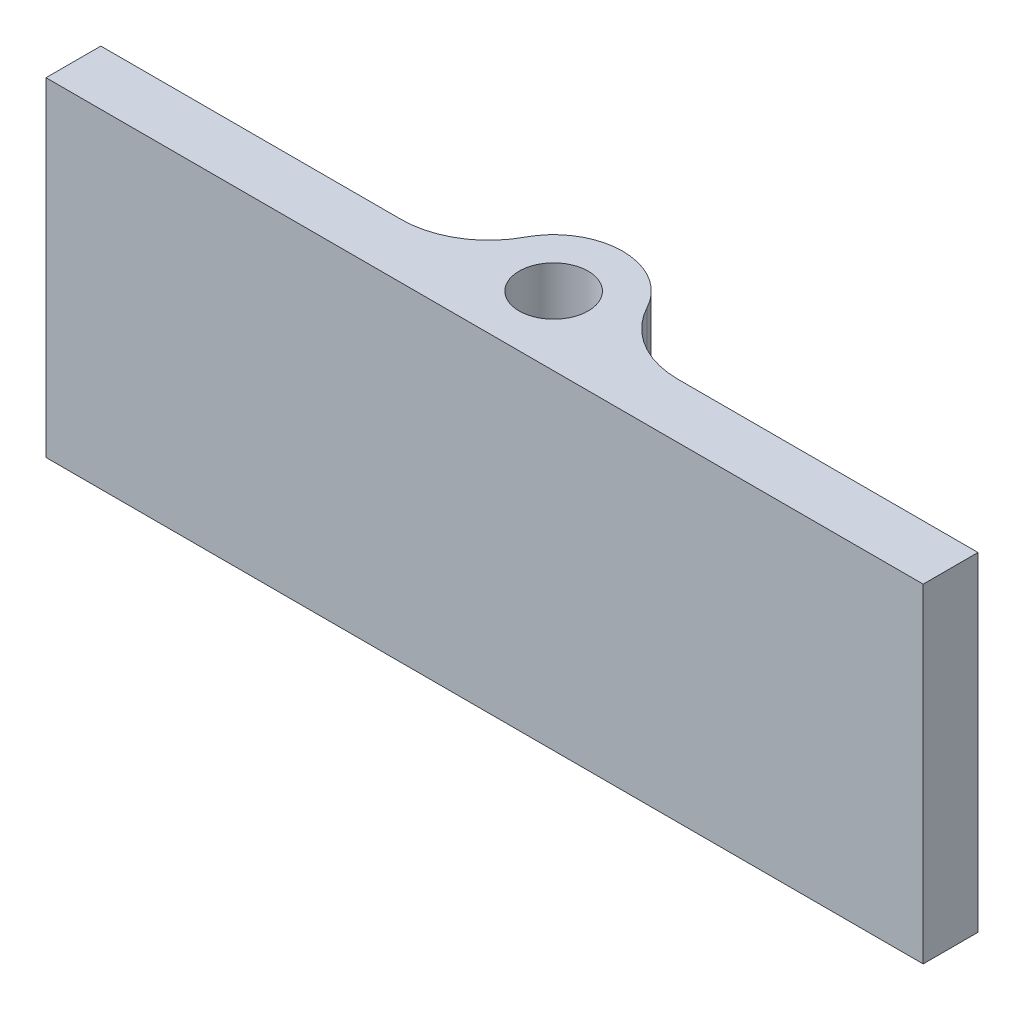
SolidWorks part; units mm, degrees
material "LWPLA"
ref_plane "Front Plane" through (0, 0, 0) normal (0, 0, 1) x (1, 0, 0)
ref_plane "Top Plane" through (0, 0, 0) normal (0, 1, 0) x (1, 0, 0)
ref_plane "Right Plane" through (0, 0, 0) normal (1, 0, 0) x (0, 0, -1)
sketch "Sketch1" plane through (0, 0, 0) normal (0, 1, 0) x (1, 0, 0)
  line L0 (-12.7, -2) -> (12.7, -2)
  line L1 (-12.7, -2) -> (-12.7, -0.4125)
  line L2 (-12.7, -0.4125) -> (-1.957, -0.4125)
  line L3 (0, -2) -> (0, 2) construction
  line L4 (12.7, -2) -> (12.7, -0.4125)
  line L5 (12.7, -0.4125) -> (1.957, -0.4125)
  circle A0 centre (0, 0) radius 1
  circle A1 centre (0, 0) radius 2
  point P7 (0, -2)
  dimension "D1" = 2
  dimension "D2" = 4
  dimension "D3" = 25.4
  dimension "D4" = 1.5875
extrude "Boss-Extrude1" add sketch "Sketch1" along normal blind 9.525 contours A1 L2 L1 L0 | A1 L0 L4 L5 | L3 A1 A0 | A1 L3 A0
fillet "Fillet1" radius 2.54 2 edges at (-1.957, 4.7625, 0.4125) (1.957, 4.7625, 0.4125)
